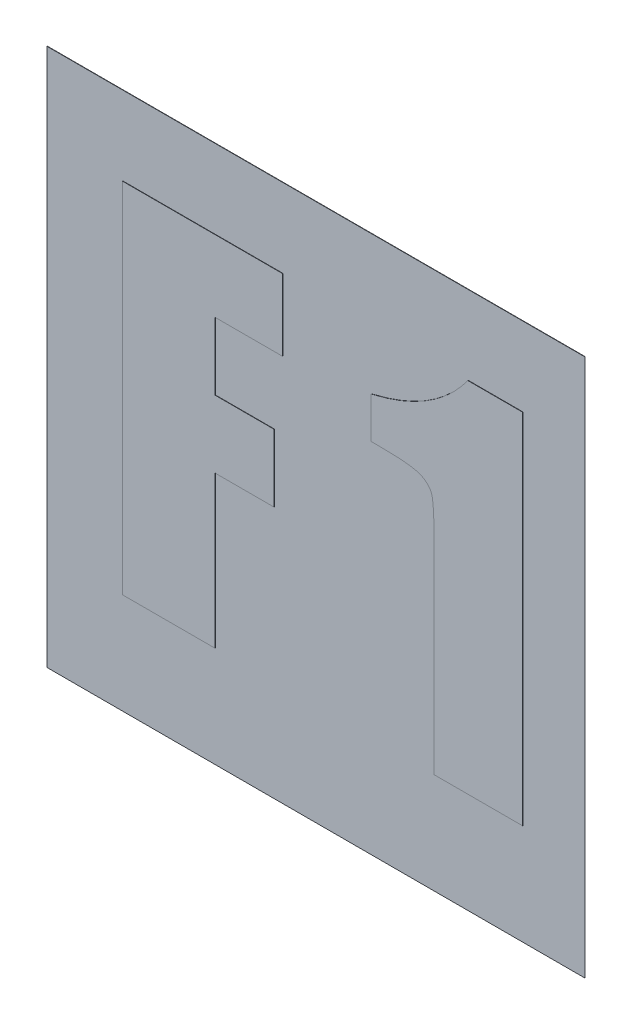
SolidWorks part; units mm, degrees
ref_plane "Plane1" through (0, 0, 0) normal (0, 0, 1) x (1, 0, 0)
ref_plane "Plane2" through (0, 0, 0) normal (0, 1, 0) x (1, 0, 0)
ref_plane "Plane3" through (0, 0, 0) normal (1, 0, 0) x (0, 0, -1)
sketch "Sketch1" plane through (0, 0, 0) normal (0, 0, 1) x (1, 0, 0)
  line L0 (-69.0098, 0) -> (69.0098, 0) construction
  line L1 (0, 52.3212) -> (0, -57.1323) construction
  line L2 (-7.5, 7.5) -> (7.5, 7.5)
  line L3 (-7.5, 7.5) -> (-7.5, -7.5)
  line L4 (7.5, 7.5) -> (7.5, -7.5)
  line L5 (-7.5, -7.5) -> (7.5, -7.5)
  point P8 (0, -7.5)
  point P11 (0, 7.5)
  point P12 (7.5, 0)
  point P13 (-7.5, 0)
  dimension "D1" = 15
  dimension "D2" = 15
extrude "Base-Extrude" add sketch "Sketch1" along normal blind 0.01
sketch "Sketch3" plane through (0, 0, 0.01) normal (0, 0, 1) x (1, 0, 0)
  text T0 "F 1" font "Impact" height in points 36
extrude "Boss-Extrude1" add sketch "Sketch3" along normal blind 0.01
